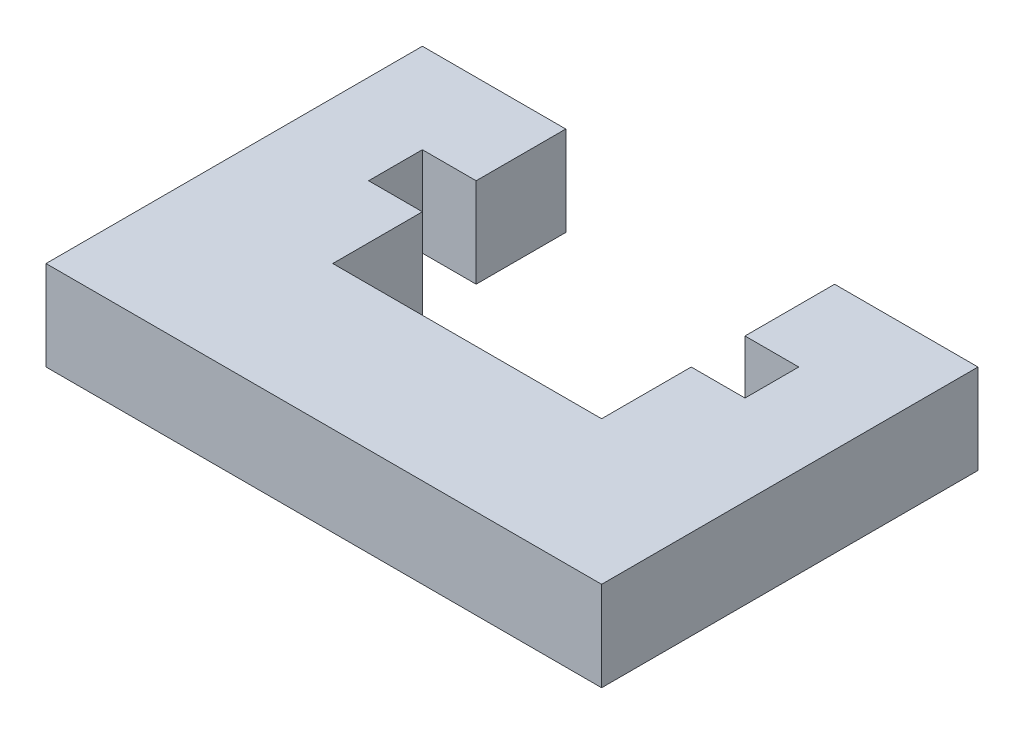
SolidWorks part; units mm, degrees
ref_plane "前视基准面" through (0, 0, 0) normal (0, 0, 1) x (1, 0, 0)
ref_plane "上视基准面" through (0, 0, 0) normal (0, 1, 0) x (1, 0, 0)
ref_plane "右视基准面" through (0, 0, 0) normal (1, 0, 0) x (0, 0, -1)
sketch "草图1" plane through (0, 0, 0) normal (0, 1, 0) x (1, 0, 0)
  line L0 (0, 21) -> (0, 0)
  line L1 (0, 0) -> (31, 0)
  line L2 (31, 0) -> (31, 21)
  line L3 (31, 21) -> (23, 21)
  line L4 (23, 21) -> (23, 8)
  line L5 (23, 8) -> (8, 8)
  line L6 (8, 8) -> (8, 21)
  line L7 (8, 21) -> (0, 21)
  point P7 (-3.5821, -10.9328)
  point P9 (0, 0)
  dimension "D1" = 8
  dimension "D2" = 8
  dimension "D3" = 15
  dimension "D4" = 8
  dimension "D5" = 21
  dimension "D6" = 21
extrude "凸台-拉伸1" add sketch "草图1" along normal blind 5
sketch "草图2" plane through (0, 5, 0) normal (0, 1, 0) x (1, 0, 0)
  line L1 (26, 16) -> (5, 16)
  line L2 (26, 16) -> (26, 13)
  line L3 (26, 13) -> (5, 13)
  line L4 (5, 16) -> (5, 13)
  line L5 (26, 16) -> (5, 13) construction
  line L6 (26, 13) -> (5, 16) construction
  line L7 (8, 8) -> (8, 21) construction
  line L8 (23, 8) -> (8, 8) construction
  point P4 (15.5, 14.5)
  dimension "D1" = 21
  dimension "D2" = 3
  dimension "D3" = 3
  dimension "D4" = 5
extrude "切除-拉伸1" cut sketch "草图2" against normal up to next
